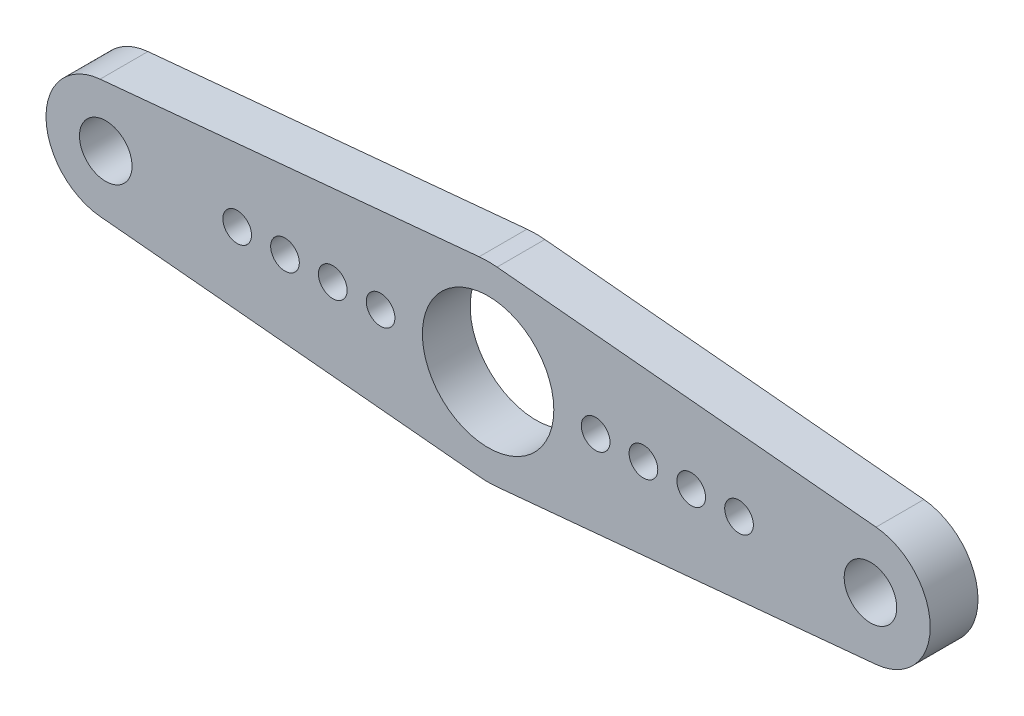
SolidWorks part; units mm, degrees
other "标注1"
sketch "草图3"
ref_plane "前视基准面" through (0, 0, 0) normal (0, 0, 1) x (1, 0, 0)
ref_plane "上视基准面" through (0, 0, 0) normal (0, 1, 0) x (1, 0, 0)
ref_plane "右视基准面" through (0, 0, 0) normal (1, 0, 0) x (0, 0, -1)
sketch "草图1" plane through (0, 0, 0) normal (0, 0, 1) x (1, 0, 0)
  line L0 (-16.2344, 2.489) -> (-0.375, 3.9824)
  line L1 (-16.2344, -2.489) -> (-0.375, -3.9824)
  line L2 (-16, 0) -> (0, 0) construction
  line L3 (0, 0) -> (0, -1.7372) construction
  line L4 (16.2344, -2.489) -> (0.375, -3.9824)
  line L5 (16.2344, 2.489) -> (0.375, 3.9824)
  arc A0 (-0.375, -3.9824) -> (0.375, -3.9824) centre (0, 0) ccw
  arc A1 (-16.2344, 2.489) -> (-16.2344, -2.489) centre (-16, 0) ccw
  arc A3 (16.2344, 2.489) -> (16.2344, -2.489) centre (16, 0) cw
  arc A4 (0.375, 3.9824) -> (-0.375, 3.9824) centre (0, 0) ccw
  dimension "D1" = 8
  dimension "D3" = 5
  dimension "D2" = 16
extrude "凸台-拉伸1" add sketch "草图1" along normal blind 2
sketch "草图2" plane through (0, 0, 2) normal (0, 0, 1) x (1, 0, 0)
  line L0 (0, 0) -> (0, -1.6575) construction
  circle A0 centre (0, 0) radius 2.75
  circle A1 centre (-16, 0) radius 1.1
  circle A2 centre (16, 0) radius 1.1
  circle A3 centre (-4.5, 0) radius 0.6
  circle A4 centre (-6.5, 0) radius 0.6
  circle A5 centre (-8.5, 0) radius 0.6
  circle A6 centre (-10.5, 0) radius 0.6
  circle A7 centre (4.5, 0) radius 0.6
  circle A8 centre (10.5, 0) radius 0.6
  circle A9 centre (8.5, 0) radius 0.6
  circle A10 centre (6.5, 0) radius 0.6
  dimension "D1" = 5.5
  dimension "D2" = 2.2
  dimension "D4" = 1.2
  dimension "D3" = 4.5
  dimension "D5" = 4
extrude "切除-拉伸1" cut sketch "草图2" against normal up to surface (2 mm away) up to face at (0, 0, 0)
